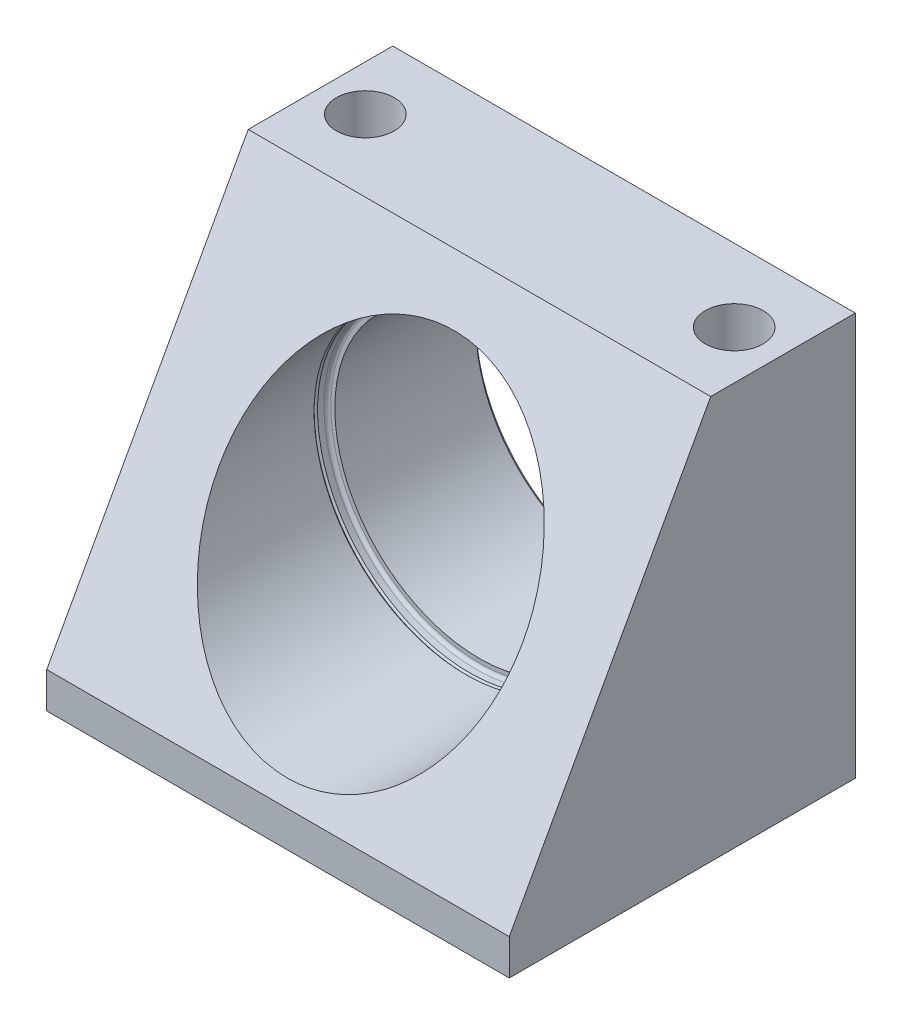
SolidWorks part; units mm, degrees
material "Alloy Steel"
ref_plane "Front Plane" through (0, 0, 0) normal (0, 0, 1) x (1, 0, 0)
ref_plane "Top Plane" through (0, 0, 0) normal (0, 1, 0) x (1, 0, 0)
ref_plane "Right Plane" through (0, 0, 0) normal (1, 0, 0) x (0, 0, -1)
sketch "Sketch1" plane through (0, 0, 0) normal (0, 0, 1) x (1, 0, 0)
  line L0 (50.8, 45.0088) -> (50.8, 88.4936) construction
  line L1 (0, 88.4936) -> (101.6, 88.4936)
  line L2 (0, 88.4936) -> (0, 0)
  line L3 (0, 0) -> (101.6, 0)
  line L4 (101.6, 88.4936) -> (101.6, 0)
  circle A0 centre (50.8, 45.0088) radius 31.7627
  dimension "D4" = 63.5254
  dimension "D1" = 101.6
  dimension "D2" = 88.4936
  dimension "D3" = 45.0088
extrude "Extrude1" add sketch "Sketch1" against normal blind 75.9968
sketch "Sketch2" plane through (101.6, 0, 0) normal (1, 0, 0) x (0, 0, -1)
  line L0 (0, 88.4936) -> (44.2468, 88.4936)
  line L3 (75.9968, 88.4936) -> (0, 88.4936) construction
  line L4 (44.2468, 88.4936) -> (0, 7.874)
  line L5 (0, 0) -> (0, 88.4936) construction
  line L6 (0, 7.874) -> (0, 88.4936)
  line L7 (75.9968, 0) -> (75.9968, 88.4936) construction
  line L8 (75.9968, 0) -> (0, 0) construction
  dimension "D2" = 7.874
  dimension "D1" = 31.75
extrude "Cut-Extrude1" cut sketch "Sketch2" against normal through all
sketch "Sketch3" plane through (0, 0, 0) normal (0, 0, -1) x (-1, 0, 0)
  circle A0 centre (-50.8, 45.0088) radius 33.401
  dimension "D1" = 66.802
extrude "Cut-Extrude2" cut sketch "Sketch3" along normal offset from surface (44.2468 mm away) 31.75 up to face at (82.5627, 45.0088, -75.9968)
fillet "Fillet1" radius 0.762 1 edges at (84.201, 45.0088, -44.2468)
hole_wizard "Hole1" positions "Sketch5" profile "Sketch4" legacy end condition up to next
sketch "Sketch5" plane through (0, 88.4936, 0) normal (0, 1, 0) x (-1, 0, 0)
  line L0 (-101.6, -75.9968) -> (-101.6, -44.2468) construction
  line L2 (-101.6, -75.9968) -> (0, -75.9968) construction
  point P0 (-9.9822, -59.9948)
  point P1 (-91.0082, -59.9948)
  dimension "D1" = 10.5918
  dimension "D2" = 16.002
  dimension "D3" = 81.026
sketch "Sketch4" plane through (9.9822, 88.4936, -59.9948) normal (1, 0, 0) x (0, 0, 1)
  line L0 (0, 0) -> (0, 88.4936)
  line L1 (0, 88.4936) -> (6.35, 88.4936)
  line L2 (6.35, 88.4936) -> (6.35, 0)
  line L3 (6.35, 0) -> (0, 0)
  line L4 (0, 110) -> (0, -10) construction
  dimension "Diameter" = 12.7
  dimension "Depth" = 88.4936
ref_plane "Plane1" through (0, 45.0088, 0) normal (0, 1, 0) x (-1, 0, 0)
sketch "Sketch6" plane through (0, 45.0088, 0) normal (0, 1, 0) x (-1, 0, 0)
  line L0 (-17.399, -41.3258) -> (-17.399, -42.0878)
  line L1 (-17.399, -43.4848) -> (-17.399, -20.3809) construction
  line L2 (-17.399, -42.0878) -> (-17.018, -41.7068)
  line L3 (-17.018, -41.7068) -> (-17.399, -41.3258)
  line L4 (-50.8, 17.5081) -> (-50.8, -67.5449) construction
  line L5 (-50.8, -75.9968) -> (-50.8, -44.2468) construction
  line L6 (-101.6, -75.9968) -> (0, -75.9968) construction
  line L7 (-19.0373, -75.2475) -> (-19.0373, -75.9968)
  line L9 (-19.0373, -75.9968) -> (-18.288, -75.9968)
  line L10 (-18.288, -75.9968) -> (-19.0373, -75.2475)
  line L12 (-19.0373, -75.9968) -> (-19.0373, -44.2468) construction
  dimension "D1" = 90
  dimension "D2" = 45
  dimension "D3" = 0.762
  dimension "D4" = 34.29
  dimension "D5" = 45
  dimension "D6" = 65.024
revolve "Cut-Revolve1" cut sketch "Sketch6" angle 360 about L4
